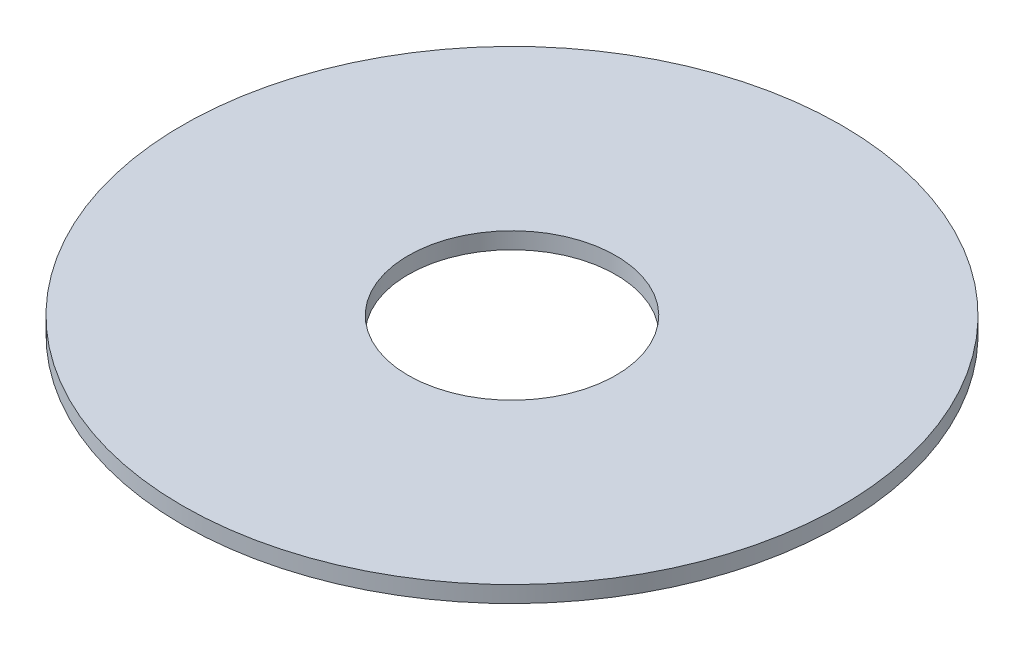
SolidWorks part; units mm, degrees
ref_plane "Front Plane" through (0, 0, 0) normal (0, 0, 1) x (1, 0, 0)
ref_plane "Top Plane" through (0, 0, 0) normal (0, 1, 0) x (1, 0, 0)
ref_plane "Right Plane" through (0, 0, 0) normal (1, 0, 0) x (0, 0, -1)
sketch "Sketch3" plane through (0, 0, 0) normal (0, 1, 0) x (1, 0, 0)
  circle A0 centre (0, 0) radius 100
  circle A1 centre (0, 0) radius 31.5
  dimension "D1" = 200
  dimension "D2" = 63
extrude "Boss-Extrude2" add sketch "Sketch3" along normal blind 5
